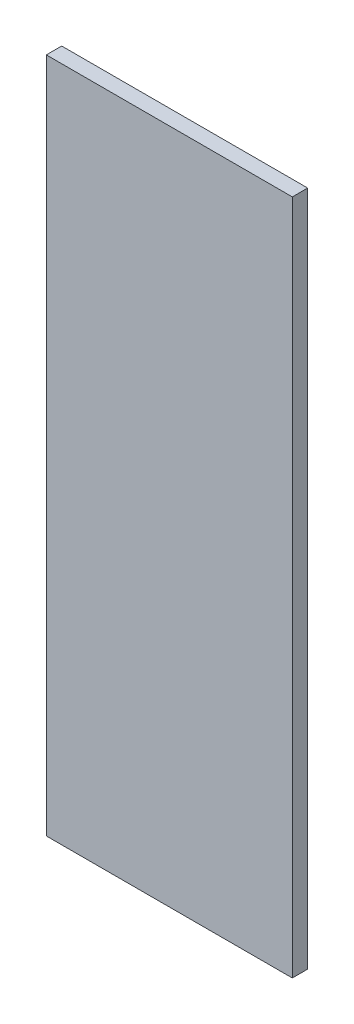
SolidWorks part; units mm, degrees
ref_plane "Front Plane" through (0, 0, 0) normal (0, 0, 1) x (1, 0, 0)
ref_plane "Top Plane" through (0, 0, 0) normal (0, 1, 0) x (1, 0, 0)
ref_plane "Right Plane" through (0, 0, 0) normal (1, 0, 0) x (0, 0, -1)
sketch "Sketch1" plane through (0, 0, 0) normal (0, 0, 1) x (1, 0, 0)
  line L1 (0, 0) -> (50.8, 0)
  line L2 (0, 0) -> (0, 139.7)
  line L3 (0, 139.7) -> (50.8, 139.7)
  line L4 (50.8, 0) -> (50.8, 139.7)
  dimension "D1" = 50.8
  dimension "D2" = 139.7
extrude "Boss-Extrude1" add sketch "Sketch1" along normal blind 3.175
